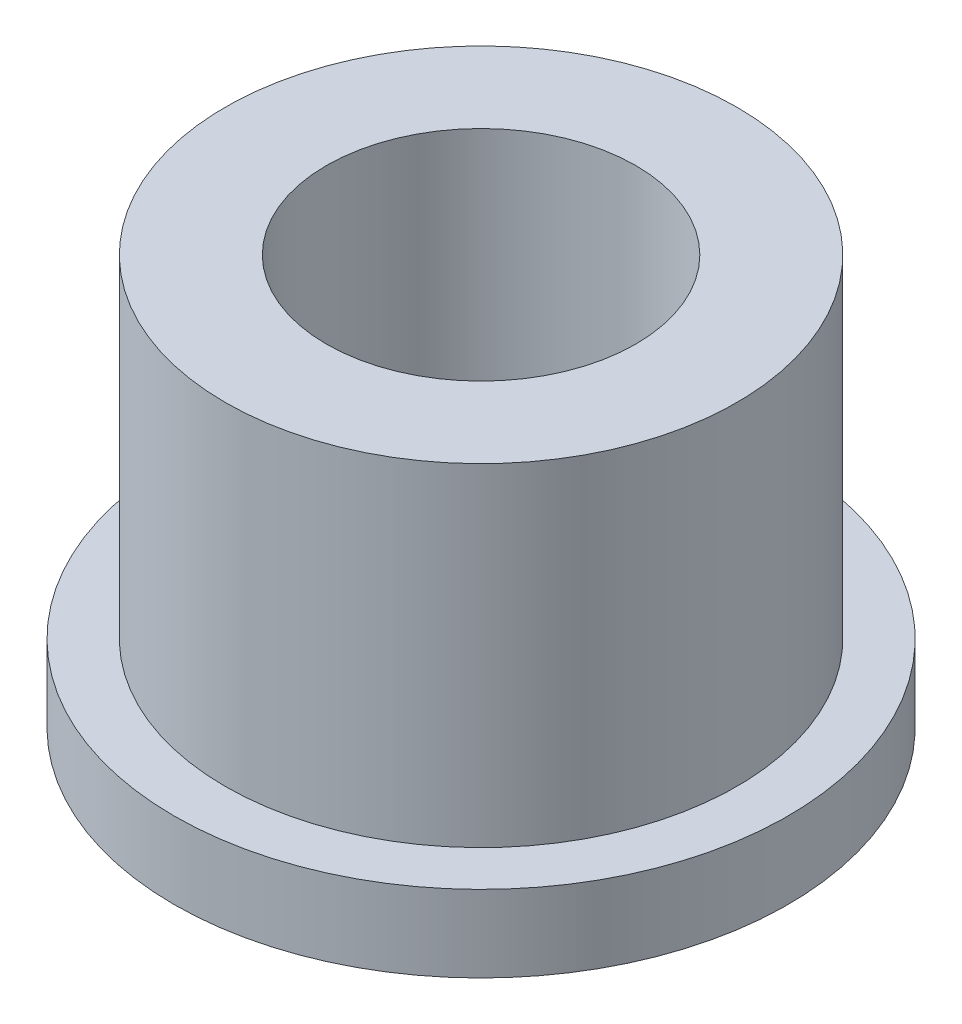
SolidWorks part; units mm, degrees
ref_plane "Front" through (0, 0, 0) normal (0, 0, 1) x (1, 0, 0)
ref_plane "Top" through (0, 0, 0) normal (0, 1, 0) x (1, 0, 0)
ref_plane "Right" through (0, 0, 0) normal (1, 0, 0) x (0, 0, -1)
sketch "Sketch1" plane through (0, 0, 0) normal (0, 1, 0) x (1, 0, 0)
  circle A0 centre (0, 0) radius 2.4003
  circle A1 centre (0, 0) radius 3.9688
  circle A2 centre (0, 0) radius 4.7625
  dimension "ID" = 4.8006
  dimension "OD" = 7.9375
  dimension "FlangeOD" = 9.525
sketch "Sketch2" plane through (0, 0, 0) normal (0, 1, 0) x (1, 0, 0)
  circle A0 centre (0, 0) radius 2.4003 construction
  circle A1 centre (0, 0) radius 3.9688 construction
  circle A2 centre (0, 0) radius 2.4003
  circle A3 centre (0, 0) radius 3.9688
extrude "Boss-Extrude1" add sketch "Sketch2" along normal blind 6.35
sketch "Sketch3" plane through (0, 0, 0) normal (0, 1, 0) x (1, 0, 0)
  circle A0 centre (0, 0) radius 4.7625 construction
  circle A1 centre (0, 0) radius 3.9688 construction
  circle A2 centre (0, 0) radius 4.7625
  circle A3 centre (0, 0) radius 3.9688
extrude "Boss-Extrude2" add sketch "Sketch3" along normal blind 1.1906
